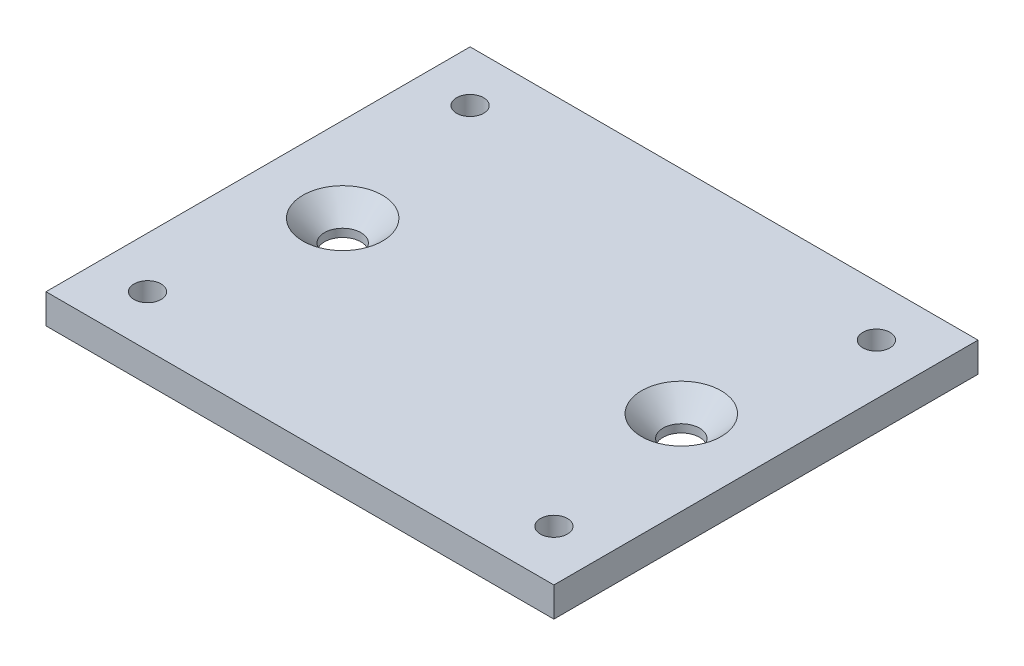
SolidWorks part; units mm, degrees
ref_plane "Front" through (0, 0, 0) normal (0, 0, 1) x (1, 0, 0)
ref_plane "Top" through (0, 0, 0) normal (0, 1, 0) x (1, 0, 0)
ref_plane "Right" through (0, 0, 0) normal (1, 0, 0) x (0, 0, -1)
sketch "Sketch1" plane through (0, 0, 0) normal (0, 1, 0) x (1, 0, 0)
  line L0 (-30, 21.05) -> (-30, -21.05)
  line L1 (-24, 19.05) -> (24, 19.05)
  line L2 (-24, 19.05) -> (-24, -19.05)
  line L3 (-24, -19.05) -> (24, -19.05)
  line L4 (24, 19.05) -> (24, -19.05)
  line L5 (-24, 19.05) -> (24, -19.05) construction
  line L6 (-24, -19.05) -> (24, 19.05) construction
  line L7 (-26, -25.05) -> (26, -25.05)
  line L8 (30, 21.05) -> (30, -21.05)
  line L9 (-26, 25.05) -> (26, 25.05)
  line L10 (-30, 25.05) -> (-30, -25.05) construction
  line L11 (-30, -25.05) -> (30, -25.05) construction
  line L12 (30, 25.05) -> (30, -25.05) construction
  line L13 (-30, 25.05) -> (30, 25.05) construction
  line L14 (0, 19.05) -> (0, -19.05) construction
  line L15 (-30, 0) -> (30, 0) construction
  line L16 (-30, 21.05) -> (-30, 25.05)
  line L17 (-30, 25.05) -> (-26, 25.05)
  line L19 (-26, -25.05) -> (-30, -25.05)
  line L20 (-30, -25.05) -> (-30, -21.05)
  line L21 (30, -21.05) -> (30, -25.05)
  line L22 (30, -25.05) -> (26, -25.05)
  line L24 (26, 25.05) -> (30, 25.05)
  line L25 (30, 25.05) -> (30, 21.05)
  circle A0 centre (-24, 19.05) radius 1.5
  circle A1 centre (-24, -19.05) radius 1.5
  circle A2 centre (24, -19.05) radius 1.5
  circle A3 centre (24, 19.05) radius 1.5
  circle A16 centre (-20, 0) radius 0.5
  circle A17 centre (20, 0) radius 0.5
  point P0 (0, 0)
  point P26 (0, 10)
  point P29 (0, 0)
  point P34 (0, -10)
  point P66 (0, 0)
  dimension "D4" = 3
  dimension "D5" = 3
  dimension "D6" = 3
  dimension "D7" = 3
  dimension "D14" = 1
  dimension "D15" = 1
  dimension "D1" = 48
  dimension "D2" = 38.1
  dimension "D9" = 10
  dimension "D10" = 10
  dimension "D16" = 20
  dimension "D17" = 20
  dimension "D3" = 6
extrude "Boss-Extrude2" add sketch "Sketch1" along normal blind 3.5
hole_wizard "M3 Clearance Hole1" positions "Sketch2" profile "Sketch3" hole size "M3" standard "ANSI Metric" end condition up to next
sketch "Sketch2" plane through (0, 3.5, 0) normal (0, 1, 0) x (1, 0, 0)
  point P0 (-24, 19.05)
  point P3 (24, 19.05)
  point P6 (24, -19.05)
  point P9 (-24, -19.05)
sketch "Sketch3" plane through (-24, 3.5, -19.05) normal (1, 0, 0) x (0, 0, 1)
  line L0 (0, 0) -> (0, 3.5)
  line L1 (0, 3.5) -> (1.6, 3.5)
  line L2 (1.6, 3.5) -> (1.6, 0)
  line L5 (1.6, 0) -> (0, 0)
  line L11 (0, -6.35) -> (0, 107.95) construction
  dimension "Thru Hole Dia." = 3.2
  dimension "Thru Hole Depth" = 3.5
hole_wizard "CSK for M4 Flat Head Machine Screw1" positions "Sketch4" profile "Sketch5" countersink size "M4" standard "ANSI Metric" end condition up to next
sketch "Sketch4" plane through (0, 3.5, 0) normal (0, 1, 0) x (1, 0, 0)
  point P0 (-20, 0)
  point P3 (20, 0)
sketch "Sketch5" plane through (-20, 3.5, 0) normal (1, 0, 0) x (0, 0, 1)
  line L0 (0, 0) -> (0, 3.5)
  line L1 (0, 3.5) -> (2.15, 3.5)
  line L2 (2.15, 3.5) -> (2.15, 2.55)
  line L3 (2.15, 2.55) -> (4.7, 0)
  line L5 (4.7, 0) -> (0, 0)
  line L6 (-2.15, 2.55) -> (-4.7, 0) construction
  line L11 (0, -6.35) -> (0, 107.95) construction
  dimension "Thru Hole Dia." = 4.3
  dimension "Thru Hole Depth" = 3.5
  dimension "Near C'Sink Dia." = 9.4
  dimension "Near C'Sink Angle" = 90
